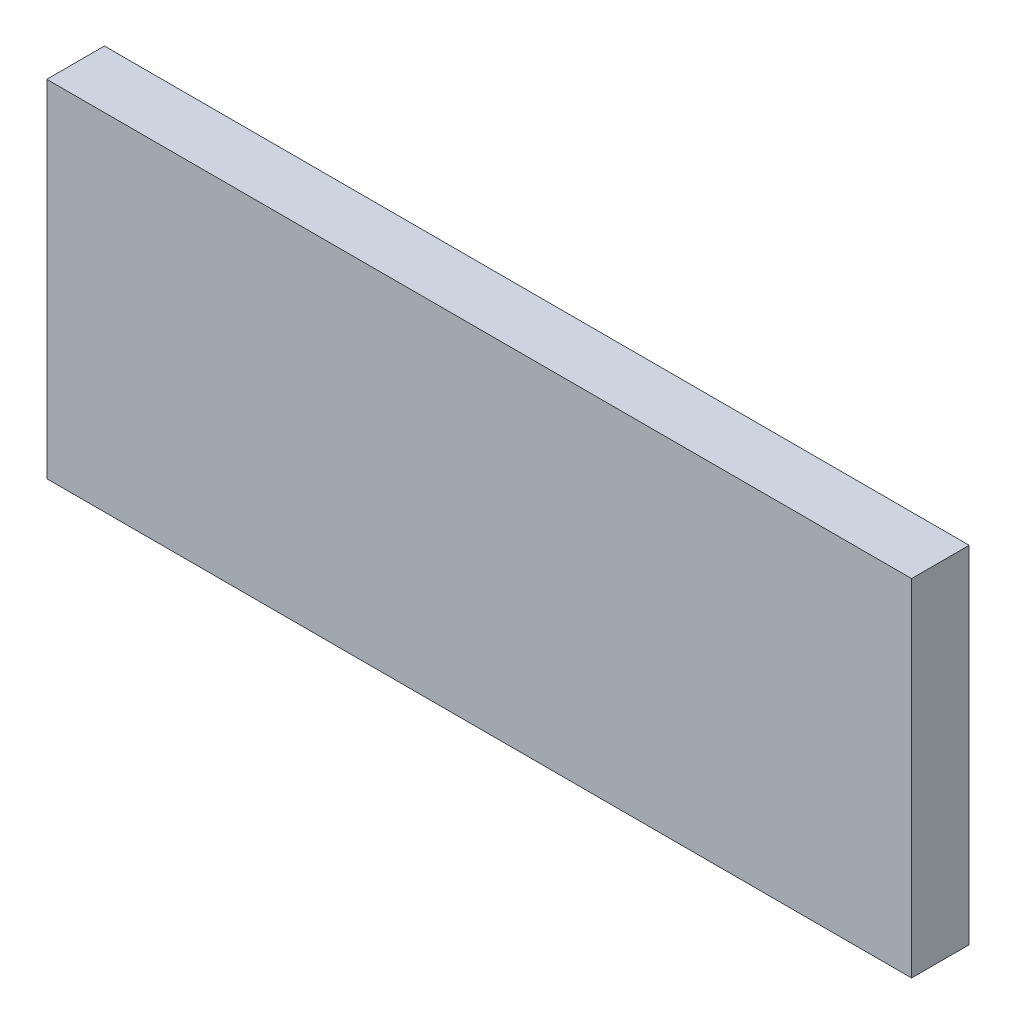
SolidWorks part; units mm, degrees
ref_plane "Front Plane" through (0, 0, 0) normal (0, 0, 1) x (1, 0, 0)
ref_plane "Top Plane" through (0, 0, 0) normal (0, 1, 0) x (1, 0, 0)
ref_plane "Right Plane" through (0, 0, 0) normal (1, 0, 0) x (0, 0, -1)
sketch "Sketch1" plane through (0, 0, 0) normal (0, 0, 1) x (1, 0, 0)
  line L1 (-171.9889, 2.1188) -> (-95.7889, 2.1188)
  line L2 (-171.9889, 2.1188) -> (-171.9889, -28.3612)
  line L3 (-171.9889, -28.3612) -> (-95.7889, -28.3612)
  line L4 (-95.7889, 2.1188) -> (-95.7889, -28.3612)
  line L5 (-171.9889, 2.1188) -> (-95.7889, -28.3612) construction
  line L6 (-171.9889, -28.3612) -> (-95.7889, 2.1188) construction
  point P0 (-133.8889, -13.1212)
extrude "Boss-Extrude1" add sketch "Sketch1" along normal blind 5.08
